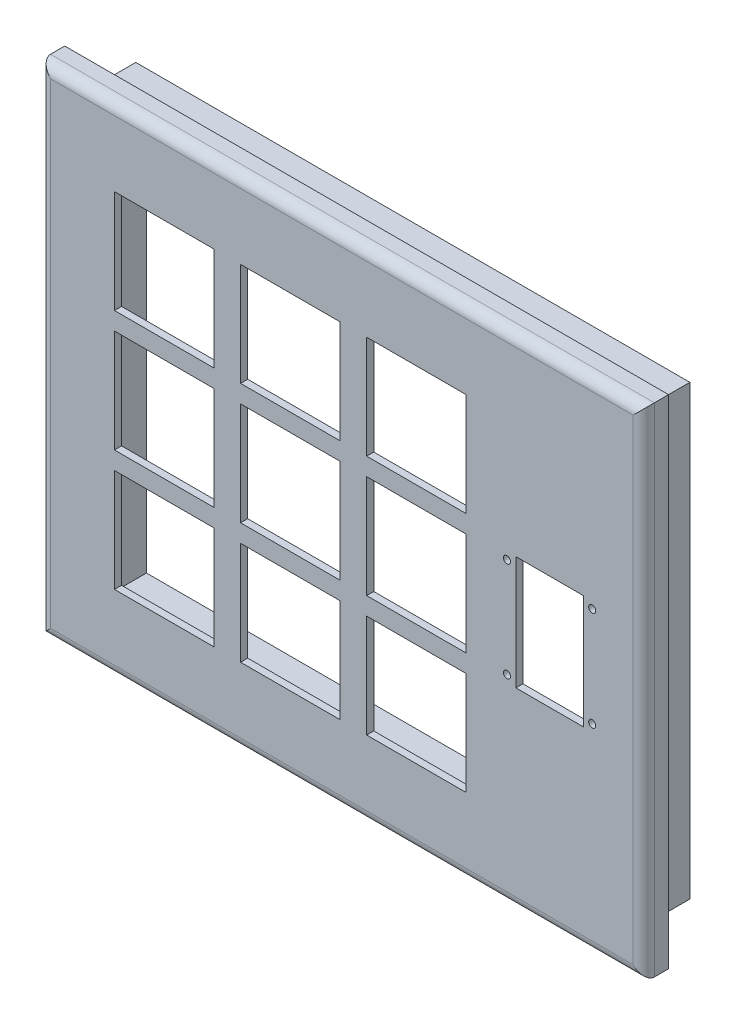
SolidWorks part; units mm, degrees
ref_plane "Alzado" through (0, 0, 0) normal (0, 0, 1) x (1, 0, 0)
ref_plane "Planta" through (0, 0, 0) normal (0, 1, 0) x (1, 0, 0)
ref_plane "Vista lateral" through (0, 0, 0) normal (1, 0, 0) x (0, 0, -1)
sketch "Croquis1" plane through (0, 0, 0) normal (0, 0, 1) x (1, 0, 0)
  line L1 (-85, 70) -> (85, 70)
  line L2 (-85, 70) -> (-85, -70)
  line L3 (-85, -70) -> (85, -70)
  line L4 (85, 70) -> (85, -70)
  line L5 (-85, 70) -> (85, -70) construction
  line L6 (-85, -70) -> (85, 70) construction
  point P0 (0, 0)
  dimension "D1" = 170
  dimension "D2" = 140
extrude "Saliente-Extruir1" add sketch "Croquis1" along normal blind 20
sketch "Croquis2" plane through (0, 0, 0) normal (0, 0, -1) x (-1, 0, 0)
  line L8 (-78, 63) -> (-78, -63)
  line L9 (-78, -63) -> (78, -63)
  line L10 (78, -63) -> (78, 63)
  line L11 (78, 63) -> (-78, 63)
  line L12 (-78, 63) -> (-78, -63)
  line L13 (-78, -63) -> (78, -63)
  line L14 (78, -63) -> (78, 63)
  line L15 (78, 63) -> (-78, 63)
  line L20 (-85, 70) -> (-85, -70)
  line L21 (-85, -70) -> (85, -70)
  line L22 (85, -70) -> (85, 70)
  line L23 (85, 70) -> (-85, 70)
  line L24 (-85, 70) -> (-85, -70)
  line L25 (-85, -70) -> (85, -70)
  line L26 (85, -70) -> (85, 70)
  line L27 (85, 70) -> (-85, 70)
  dimension "D1" = 7
  dimension "D2" = 0
extrude "Cortar-Extruir1" cut sketch "Croquis2" against normal blind 13
sketch "Croquis3" plane through (0, 0, 0) normal (0, 0, -1) x (-1, 0, 0)
  line L8 (75, 60) -> (-75, 60)
  line L9 (-75, 60) -> (-75, -60)
  line L10 (-75, -60) -> (75, -60)
  line L11 (75, -60) -> (75, 60)
  line L12 (75, 60) -> (-75, 60)
  line L13 (-75, 60) -> (-75, -60)
  line L14 (-75, -60) -> (75, -60)
  line L15 (75, -60) -> (75, 60)
  dimension "D1" = 3
extrude "Cortar-Extruir2" cut sketch "Croquis3" against normal blind 18
sketch "Croquis4" plane through (0, 0, 18) normal (0, 0, -1) x (-1, 0, 0)
  line L0 (-75, -60) -> (75, -60) construction
  line L1 (36, -48.5) -> (64, -48.5)
  line L2 (36, -48.5) -> (36, -19.5)
  line L3 (36, -19.5) -> (64, -19.5)
  line L4 (64, -48.5) -> (64, -19.5)
  line L5 (75, -60) -> (75, 60) construction
  line L6 (75, -60) -> (75, 60) construction
  line L7 (36, -14.5) -> (64, -14.5)
  line L8 (36, -14.5) -> (36, 14.5)
  line L9 (36, 14.5) -> (64, 14.5)
  line L10 (64, -14.5) -> (64, 14.5)
  line L13 (36, 19.5) -> (64, 19.5)
  line L14 (36, 19.5) -> (36, 48.5)
  line L15 (36, 48.5) -> (64, 48.5)
  line L16 (64, 19.5) -> (64, 48.5)
  line L17 (-75, 60) -> (-75, -60) construction
  line L18 (0.5, -14.5) -> (28.5, -14.5)
  line L19 (0.5, -14.5) -> (0.5, 14.5)
  line L20 (0.5, 14.5) -> (28.5, 14.5)
  line L21 (28.5, -14.5) -> (28.5, 14.5)
  line L23 (0.5, -48.5) -> (28.5, -48.5)
  line L24 (0.5, -48.5) -> (0.5, -19.5)
  line L25 (0.5, -19.5) -> (28.5, -19.5)
  line L26 (28.5, -48.5) -> (28.5, -19.5)
  line L27 (-35, -48.5) -> (-7, -48.5)
  line L28 (-35, -48.5) -> (-35, -19.5)
  line L29 (-35, -19.5) -> (-7, -19.5)
  line L30 (-7, -48.5) -> (-7, -19.5)
  line L31 (0.5, 19.5) -> (28.5, 19.5)
  line L32 (0.5, 19.5) -> (0.5, 48.5)
  line L33 (0.5, 48.5) -> (28.5, 48.5)
  line L34 (28.5, 19.5) -> (28.5, 48.5)
  line L35 (-35, -14.5) -> (-7, -14.5)
  line L36 (-35, -14.5) -> (-35, 14.5)
  line L37 (-35, 14.5) -> (-7, 14.5)
  line L38 (-7, -14.5) -> (-7, 14.5)
  line L39 (-35, 19.5) -> (-7, 19.5)
  line L40 (-35, 19.5) -> (-35, 48.5)
  line L41 (-35, 48.5) -> (-7, 48.5)
  line L42 (-7, 19.5) -> (-7, 48.5)
  line L51 (-68, -16) -> (-49, -16)
  line L52 (-68, -16) -> (-68, 16)
  line L53 (-68, 16) -> (-49, 16)
  line L54 (-49, -16) -> (-49, 16)
  line L55 (-68, -16) -> (-49, 16) construction
  line L56 (-68, 16) -> (-49, -16) construction
  circle A2 centre (-46.5, -14) radius 1
  circle A3 centre (-46.5, 14) radius 1
  circle A4 centre (-70.5, -14) radius 1
  circle A5 centre (-70.5, 14) radius 1
  point P28 (0.5, 0)
  point P29 (-7, 0)
  point P46 (-58.5, 0)
  point P61 (36, 0)
  dimension "D26" = 2
  dimension "D27" = 2
  dimension "D28" = 2
  dimension "D29" = 2
  dimension "D31" = 2.5
  dimension "D33" = 2.5
  dimension "D34" = 2
  dimension "D35" = 2
  dimension "D36" = 2.5
  dimension "D2" = 11
  dimension "D3" = 28
  dimension "D4" = 29
  dimension "D5" = 28
  dimension "D6" = 29
  dimension "D7" = 11
  dimension "D8" = 5
  dimension "D9" = 5
  dimension "D10" = 29
  dimension "D11" = 28
  dimension "D12" = 29
  dimension "D13" = 28
  dimension "D14" = 28
  dimension "D15" = 29
  dimension "D16" = 7.5
  dimension "D17" = 7.5
  dimension "D18" = 36
  dimension "D19" = 29
  dimension "D20" = 5
  dimension "D21" = 0
  dimension "D22" = 60
  dimension "D23" = 19
  dimension "D24" = 32
  dimension "D25" = 7
  dimension "D30" = 2
  dimension "D32" = 2
  dimension "D37" = 2.5
  dimension "D38" = 29
  dimension "D39" = 5
  dimension "D40" = 5
  dimension "D41" = 0
  dimension "D42" = 5
extrude "Cortar-Extruir3" cut sketch "Croquis4" against normal blind 18
fillet "Redondeo1" radius 3 4 edges at (0, 70, 20) (0, -70, 20) (-85, 0, 20) (85, 0, 20)
